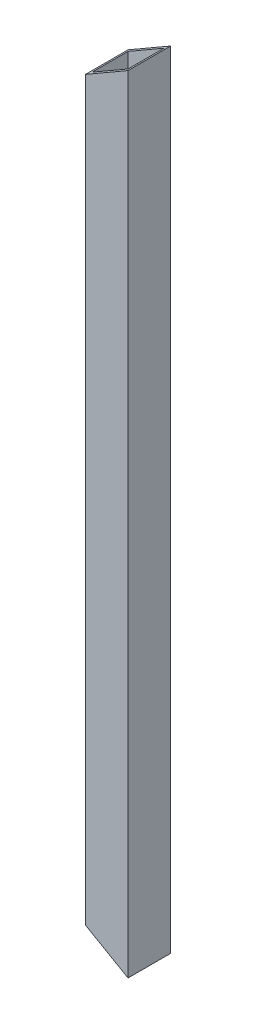
SolidWorks part; units mm, degrees
ref_plane "Front Plane" through (0, 0, 0) normal (0, 0, 1) x (1, 0, 0)
ref_plane "Top Plane" through (0, 0, 0) normal (0, 1, 0) x (1, 0, 0)
ref_plane "Right Plane" through (0, 0, 0) normal (1, 0, 0) x (0, 0, -1)
sketch "Sketch2" plane through (0, 0, 0) normal (0, 1, 0) x (1, 0, 0)
  line L0 (-6.5, 6.5) -> (6.5, 6.5)
  line L1 (-5.5, -5.5) -> (5.5, -5.5)
  line L2 (-5.5, -5.5) -> (-5.5, 5.5)
  line L3 (-5.5, 5.5) -> (5.5, 5.5)
  line L4 (5.5, -5.5) -> (5.5, 5.5)
  line L5 (-5.5, -5.5) -> (5.5, 5.5) construction
  line L6 (-5.5, 5.5) -> (5.5, -5.5) construction
  line L7 (6.5, -6.5) -> (6.5, 6.5)
  line L8 (-6.5, -6.5) -> (6.5, -6.5)
  line L9 (-6.5, -6.5) -> (-6.5, 6.5)
  point P0 (0, 0)
  dimension "D1" = 11
  dimension "D2" = 11
  dimension "D3" = 1
extrude "Boss-Extrude1" add sketch "Sketch2" along normal blind 240
sketch "Sketch3" plane through (0, 0, 6.5) normal (0, 0, 1) x (1, 0, 0)
  line L0 (6.5, 240) -> (-6.5, 232.4944)
  line L1 (-6.5, 240) -> (-6.5, 0) construction
extrude "Cut-Extrude1" cut sketch "Sketch3" against normal through all both and the other way through all flip side to cut
sketch "Sketch4" plane through (0, 0, 6.5) normal (0, 0, 1) x (1, 0, 0)
  line L0 (6.5, 0) -> (-6.5, 7.5056)
  line L1 (-6.5, 232.4944) -> (-6.5, 0) construction
  line L6 (6.5, 0) -> (6.5, 240)
  line L7 (6.5, 240) -> (-6.5, 232.4944)
  line L8 (-6.5, 232.4944) -> (-6.5, 0)
  line L9 (-6.5, 0) -> (6.5, 0)
  line L10 (6.5, 0) -> (6.5, 240)
  line L11 (6.5, 240) -> (-6.5, 232.4944)
  line L12 (-6.5, 232.4944) -> (-6.5, 7.5056)
  dimension "D1" = 0
extrude "Cut-Extrude2" cut sketch "Sketch4" against normal blind 240 flip side to cut
